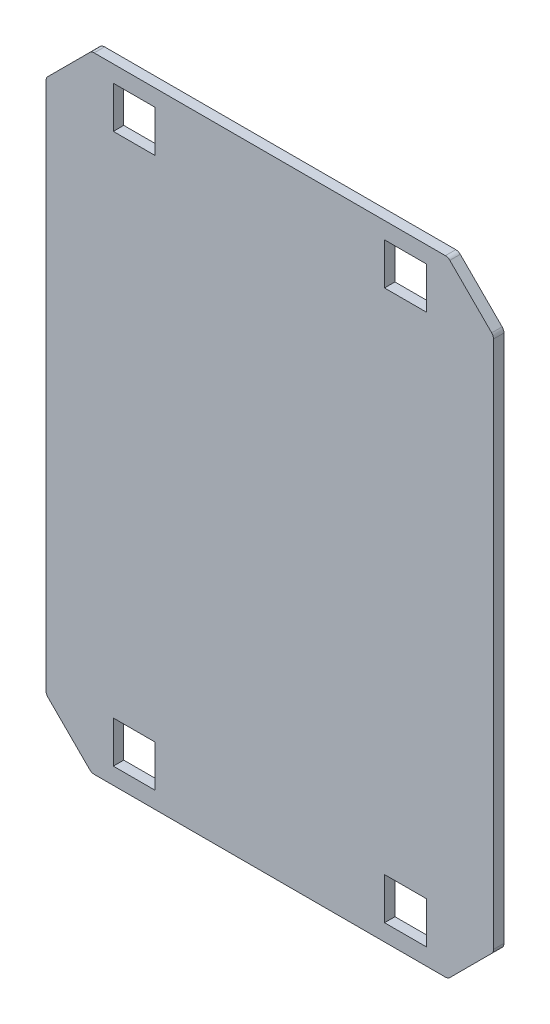
SolidWorks part; units mm, degrees
ref_plane "Plan de face" through (0, 0, 0) normal (0, 0, 1) x (1, 0, 0)
ref_plane "Plan de dessus" through (0, 0, 0) normal (0, 1, 0) x (1, 0, 0)
ref_plane "Plan de droite" through (0, 0, 0) normal (1, 0, 0) x (0, 0, -1)
sketch "Esquisse1" plane through (0, 0, 0) normal (0, 0, 1) x (1, 0, 0)
  line L0 (-112.2487, -130) -> (-87.5, -154.7487)
  line L7 (0, 154.7487) -> (0, -154.7487) construction
  line L8 (-112.2487, 0) -> (112.2487, 0) construction
  line L9 (-112.2487, 130) -> (-87.5, 154.7487)
  line L10 (112.2487, 130) -> (87.5, 154.7487)
  line L11 (112.2487, -130) -> (87.5, -154.7487)
  line L12 (-112.2487, 130) -> (-112.2487, -130)
  line L13 (-87.5, 154.7487) -> (87.5, 154.7487)
  line L14 (112.2487, 130) -> (112.2487, -130)
  line L15 (87.5, -154.7487) -> (-87.5, -154.7487)
  point P0 (0, 0)
  dimension "D1" = 260
  dimension "D2" = 175
  dimension "D3" = 35
  dimension "D4" = 135
extrude "Boss.-Extru.1" add sketch "Esquisse1" along normal blind 5
sketch "Esquisse2" plane through (0, 0, 5) normal (0, 0, 1) x (1, 0, 0)
  line L1 (-75, 141.7487) -> (-55, 141.7487)
  line L2 (-75, 141.7487) -> (-75, 121.7487)
  line L3 (-75, 121.7487) -> (-55, 121.7487)
  line L4 (-55, 141.7487) -> (-55, 121.7487)
  line L5 (-75, 141.7487) -> (-55, 121.7487) construction
  line L6 (-75, 121.7487) -> (-55, 141.7487) construction
  line L9 (0, 154.7487) -> (0, -154.7487) construction
  line L10 (-87.5, 154.7487) -> (87.5, 154.7487) construction
  line L11 (0, 154.7487) -> (0, -154.7487) construction
  line L12 (-112.2487, 0) -> (112.2487, 0) construction
  line L13 (-75, -121.7487) -> (-55, -141.7487) construction
  line L14 (-75, -141.7487) -> (-55, -121.7487) construction
  line L15 (-55, -141.7487) -> (-55, -121.7487)
  line L16 (-75, -121.7487) -> (-55, -121.7487)
  line L17 (-75, -141.7487) -> (-75, -121.7487)
  line L18 (-75, -141.7487) -> (-55, -141.7487)
  line L19 (75, -141.7487) -> (55, -121.7487) construction
  line L20 (75, -121.7487) -> (55, -141.7487) construction
  line L21 (75, -141.7487) -> (55, -141.7487)
  line L22 (75, -141.7487) -> (75, -121.7487)
  line L23 (75, -121.7487) -> (55, -121.7487)
  line L24 (55, -141.7487) -> (55, -121.7487)
  line L25 (75, 121.7487) -> (55, 141.7487) construction
  line L26 (75, 141.7487) -> (55, 121.7487) construction
  line L27 (55, 141.7487) -> (55, 121.7487)
  line L28 (75, 121.7487) -> (55, 121.7487)
  line L29 (75, 141.7487) -> (75, 121.7487)
  line L30 (75, 141.7487) -> (55, 141.7487)
  point P0 (-65, 131.7487)
  point P21 (-65, -131.7487)
  point P26 (65, -131.7487)
  point P31 (65, 131.7487)
  dimension "D1" = 65
  dimension "D2" = 23
  dimension "D3" = 20
  dimension "D4" = 20
extrude "Enlèv. mat.-Extru.1" cut sketch "Esquisse2" against normal blind 5
sketch "Esquisse3" plane through (0, 0, 5) normal (0, 0, 1) x (1, 0, 0)
  line L0 (-107.2487, 127.9289) -> (-107.2487, -127.9289)
  line L1 (-112.2487, 130) -> (-112.2487, -130) construction
  line L2 (107.2487, 127.9289) -> (107.2487, -127.9289)
  line L3 (112.2487, -130) -> (112.2487, 130) construction
  line L4 (-85.4289, 149.7487) -> (85.4289, 149.7487)
  line L5 (87.5, 154.7487) -> (-87.5, 154.7487) construction
  line L6 (-85.4289, 149.7487) -> (-107.2487, 127.9289)
  line L7 (-87.5, 154.7487) -> (-112.2487, 130) construction
  line L8 (85.4289, 149.7487) -> (107.2487, 127.9289)
  line L9 (112.2487, 130) -> (87.5, 154.7487) construction
  line L10 (-85.4289, -149.7487) -> (85.4289, -149.7487)
  line L11 (107.2487, -127.9289) -> (85.4289, -149.7487)
  line L12 (-107.2487, -127.9289) -> (-85.4289, -149.7487)
  line L13 (-87.5, -154.7487) -> (87.5, -154.7487) construction
  line L14 (87.5, -154.7487) -> (112.2487, -130) construction
  line L15 (-112.2487, -130) -> (-87.5, -154.7487) construction
  line L16 (-87.5, 154.7487) -> (-112.2487, 130)
  line L17 (-112.2487, 130) -> (-112.2487, -130)
  line L18 (-112.2487, -130) -> (-87.5, -154.7487)
  line L19 (-87.5, -154.7487) -> (87.5, -154.7487)
  line L20 (87.5, -154.7487) -> (112.2487, -130)
  line L21 (112.2487, -130) -> (112.2487, 130)
  line L22 (112.2487, 130) -> (87.5, 154.7487)
  line L23 (87.5, 154.7487) -> (-87.5, 154.7487)
  dimension "D1" = 5
  dimension "D2" = 5
  dimension "D3" = 5
  dimension "D4" = 5
  dimension "D5" = 5
  dimension "D6" = 5
  dimension "D7" = 5
  dimension "D8" = 5
extrude "Enlèv. mat.-Extru.2" cut sketch "Esquisse3" against normal blind 5
fillet "Congé1" radius 3 8 edges at (-107.2487, -127.9289, 2.5) (-85.4289, -149.7487, 2.5) (85.4289, -149.7487, 2.5) (107.2487, -127.9289, 2.5) (107.2487, 127.9289, 2.5) (85.4289, 149.7487, 2.5) (-107.2487, 127.9289, 2.5) (-85.4289, 149.7487, 2.5)
